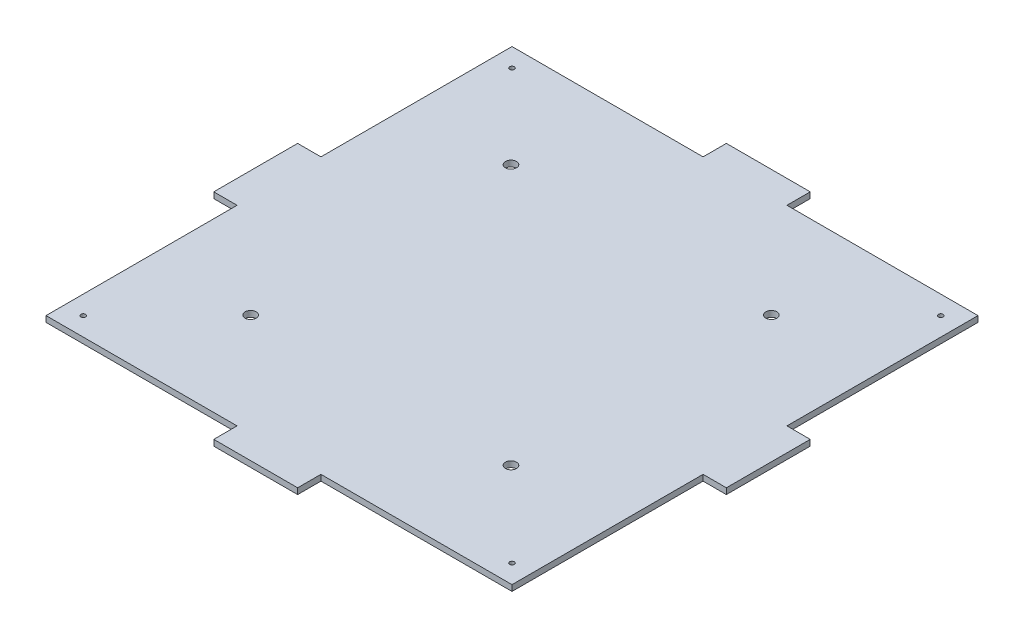
SolidWorks part; units mm, degrees
ref_plane "Front Plane" through (0, 0, 0) normal (0, 0, 1) x (1, 0, 0)
ref_plane "Top Plane" through (0, 0, 0) normal (0, 1, 0) x (1, 0, 0)
ref_plane "Right Plane" through (0, 0, 0) normal (1, 0, 0) x (0, 0, -1)
sketch "Sketch2" plane through (0, 0, 0) normal (0, 1, 0) x (1, 0, 0)
  line L1 (-125, -125) -> (125, -125)
  line L2 (-125, -125) -> (-125, 125)
  line L3 (-125, 125) -> (125, 125)
  line L4 (125, -125) -> (125, 125)
  line L5 (-125, -125) -> (125, 125) construction
  line L6 (-125, 125) -> (125, -125) construction
  point P0 (0, 0)
  dimension "D1" = 250
  dimension "250" = 250
extrude "Boss-Extrude1" add sketch "Sketch2" along normal blind 3.175
sketch "Sketch3" plane through (0, 3.175, 0) normal (0, 1, 0) x (1, 0, 0)
  line L0 (-125, 0) -> (125, 0) construction
  line L1 (-125, 125) -> (-125, -125) construction
  line L2 (125, -125) -> (125, 125) construction
  line L3 (-43.75, 125) -> (-43.75, -125) construction
  line L4 (125, 125) -> (-125, 125) construction
  line L5 (-125, -125) -> (125, -125) construction
  line L6 (0, 125) -> (0, -125) construction
  line L11 (-48.05, 28) -> (-39.45, 28)
  line L12 (-48.05, 28) -> (-48.05, 43.35)
  line L13 (-48.05, 43.35) -> (-39.45, 43.35)
  line L14 (-39.45, 28) -> (-39.45, 43.35)
  line L15 (-48.05, 28) -> (-39.45, 43.35) construction
  line L16 (-48.05, 43.35) -> (-39.45, 28) construction
  line L21 (-48.05, -43.35) -> (-39.45, -43.35)
  line L22 (-48.05, -43.35) -> (-48.05, -28)
  line L23 (-48.05, -28) -> (-39.45, -28)
  line L24 (-39.45, -43.35) -> (-39.45, -28)
  line L25 (-48.05, -43.35) -> (-39.45, -28) construction
  line L26 (-48.05, -28) -> (-39.45, -43.35) construction
  line L27 (48.05, -28) -> (39.45, -28)
  line L28 (39.45, -43.35) -> (39.45, -28)
  line L29 (48.05, -43.35) -> (39.45, -43.35)
  line L30 (48.05, -43.35) -> (48.05, -28)
  line L31 (48.05, 43.35) -> (39.45, 43.35)
  line L32 (39.45, 28) -> (39.45, 43.35)
  line L33 (48.05, 28) -> (39.45, 28)
  line L34 (48.05, 28) -> (48.05, 43.35)
  point P12 (-43.75, 35.675)
  point P17 (-43.75, -35.675)
  dimension "D1" = 43.75
  dimension "D2" = 8.6
  dimension "D3" = 15.35
  dimension "D4" = 56
  dimension "D5" = 28
sketch "Sketch10" plane through (0, 0, -125) normal (0, 0, -1) x (-1, 0, 0)
  line L0 (-125, 1.5875) -> (125, 1.5875) construction
  line L1 (-125, 3.175) -> (-125, 0) construction
  line L2 (125, 3.175) -> (125, 0) construction
  line L8 (-125, 3.175) -> (125, 3.175) construction
  line L9 (-22.5, 0) -> (22.5, 0)
  line L10 (-22.5, 0) -> (-22.5, 3.175)
  line L11 (-22.5, 3.175) -> (22.5, 3.175)
  line L12 (22.5, 0) -> (22.5, 3.175)
  line L13 (-22.5, 0) -> (22.5, 3.175) construction
  line L14 (-22.5, 3.175) -> (22.5, 0) construction
  point P6 (0, 1.5875)
  dimension "D1" = 45
extrude "Boss-Extrude2" add sketch "Sketch10" along normal blind 12.5
sketch "Sketch11" plane through (-125, 0, 0) normal (-1, 0, 0) x (0, 0, 1)
  line L0 (-125, 1.5875) -> (125, 1.5875) construction
  line L1 (-125, 3.175) -> (-125, 0) construction
  line L2 (125, 3.175) -> (125, 0) construction
  line L9 (-22.5, 0) -> (22.5, 0)
  line L10 (-22.5, 0) -> (-22.5, 3.175)
  line L11 (-22.5, 3.175) -> (22.5, 3.175)
  line L12 (22.5, 0) -> (22.5, 3.175)
  line L13 (-22.5, 0) -> (22.5, 3.175) construction
  line L14 (-22.5, 3.175) -> (22.5, 0) construction
  point P6 (0, 1.5875)
  dimension "D1" = 45
  dimension "D2" = 3.175
extrude "Boss-Extrude3" add sketch "Sketch11" along normal blind 12.5
sketch "Sketch13" plane through (0, 0, 125) normal (0, 0, 1) x (1, 0, 0)
  line L0 (-125, 1.5875) -> (125, 1.5875) construction
  line L3 (-125, 0) -> (-125, 3.175) construction
  line L9 (-22.5, 0) -> (22.5, 0)
  line L10 (-22.5, 0) -> (-22.5, 3.175)
  line L11 (-22.5, 3.175) -> (22.5, 3.175)
  line L12 (22.5, 0) -> (22.5, 3.175)
  line L13 (-22.5, 0) -> (22.5, 3.175) construction
  line L14 (-22.5, 3.175) -> (22.5, 0) construction
  line L15 (125, 3.175) -> (125, 0) construction
  point P6 (0, 1.5875)
  dimension "D1" = 45
  dimension "D2" = 3.175
extrude "Boss-Extrude4" add sketch "Sketch13" along normal blind 12.5
sketch "Sketch14" plane through (125, 0, 0) normal (1, 0, 0) x (0, 0, -1)
  line L0 (-125, 1.5875) -> (125, 1.5875) construction
  line L3 (-125, 3.175) -> (-125, 0) construction
  line L9 (-22.5, 0) -> (22.5, 0)
  line L10 (-22.5, 0) -> (-22.5, 3.175)
  line L11 (-22.5, 3.175) -> (22.5, 3.175)
  line L12 (22.5, 0) -> (22.5, 3.175)
  line L13 (-22.5, 0) -> (22.5, 3.175) construction
  line L14 (-22.5, 3.175) -> (22.5, 0) construction
  line L15 (125, 3.175) -> (125, 0) construction
  point P6 (0, 1.5875)
  dimension "D1" = 45
  dimension "D2" = 3.175
extrude "Boss-Extrude5" add sketch "Sketch14" along normal blind 12.5
hole_wizard "M3 Tapped Hole1" positions "3DSketch4" profile "Sketch20" tap size "M3" standard "ISO" end condition through all
sketch3d "3DSketch4"
  line L0 (-22.5, 3.175, -125) -> (-125, 3.175, -125) construction
  line L1 (-125, 3.175, -125) -> (-125, 3.175, -22.5) construction
  point P0 (-115, 3.175, -115)
  dimension "D1" = 10
  dimension "D2" = 10
sketch "Sketch20" plane through (-115, 3.175, -115) normal (1, 0, 0) x (0, 0, 1)
  line L0 (0, 0) -> (0, 3.175)
  line L1 (0, 3.175) -> (1.25, 3.175)
  line L2 (1.25, 3.175) -> (1.25, 0)
  line L5 (1.25, 0) -> (0, 0)
  line L11 (0, -6.35) -> (0, 107.95) construction
  dimension "Thru Tap Drill Dia." = 2.5
  dimension "Thru Tap Drill Depth" = 3.175
cosmetic thread "Hole Thread1" parameters "D2"=3
sketch "Sketch21" plane through (0, 3.175, 0) normal (0, 1, 0) x (1, 0, 0)
  line L0 (0, -137.5) -> (0, 137.5)
  line L1 (22.5, -137.5) -> (-22.5, -137.5) construction
  line L2 (-22.5, 137.5) -> (22.5, 137.5) construction
  line L3 (-137.5, 0) -> (137.5, 0)
  line L4 (-137.5, -22.5) -> (-137.5, 22.5) construction
  line L5 (137.5, 22.5) -> (137.5, -22.5) construction
  circle A0 centre (-115, 115) radius 1.25
  circle A1 centre (115, 115) radius 1.25
  circle A2 centre (115, -115) radius 1.25
  circle A3 centre (-115, -115) radius 1.25
extrude "Cut-Extrude2" cut sketch "Sketch21" against normal blind 10 contours A1 | A2 | A3
sketch "Sketch23" plane through (0, 3.175, 0) normal (0, 1, 0) x (1, 0, 0)
  line L0 (-85.2293, 0) -> (85.2293, 0)
  circle A0 centre (-70.4034, -69.85) radius 2.9718
  circle A1 centre (69.2966, -69.85) radius 2.9718
  circle A2 centre (69.2966, 69.85) radius 2.9718
  circle A3 centre (-70.4034, 69.85) radius 2.9718
  point P10 (0, 0)
  dimension "D1" = 69.85
  dimension "D2" = 139.7
  dimension "D3" = 69.85
  dimension "D4" = 139.7
  dimension "D5" = 139.7
extrude "Cut-Extrude10" cut sketch "Sketch23" against normal blind 10 contours A0 | A3 | A2 | A1
